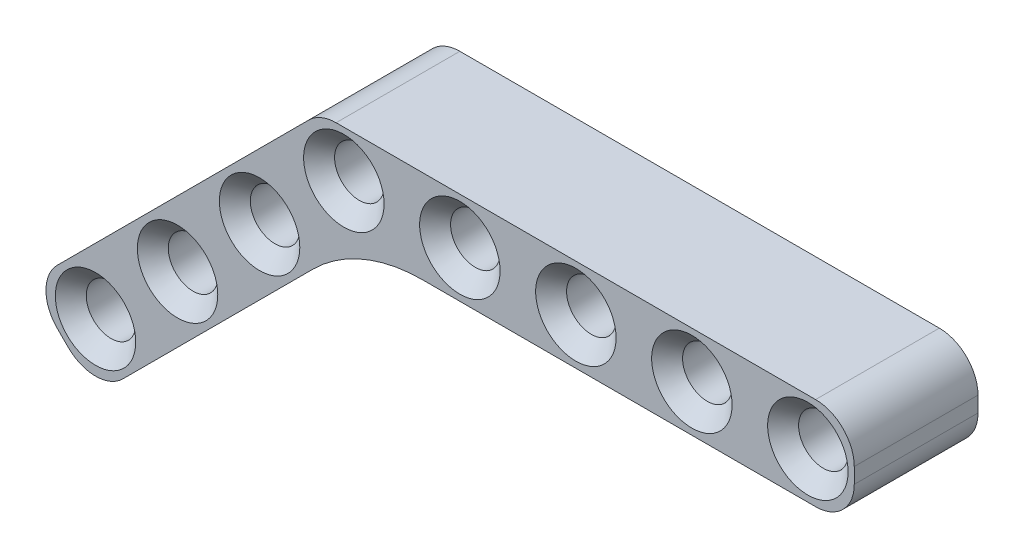
SolidWorks part; units mm, degrees
ref_plane "Front Plane" through (0, 0, 0) normal (0, 0, 1) x (1, 0, 0)
ref_plane "Top Plane" through (0, 0, 0) normal (0, 1, 0) x (1, 0, 0)
ref_plane "Right Plane" through (0, 0, 0) normal (1, 0, 0) x (0, 0, -1)
sketch "Sketch1" plane through (0, 0, 0) normal (0, 0, 1) x (1, 0, 0)
  line L1 (-0.5, 3) -> (30.5, 3)
  line L2 (-3, 0.5) -> (-3, -0.5)
  line L3 (-0.5, -3) -> (30.5, -3)
  line L4 (33, 0.5) -> (33, -0.5)
  circle A0 centre (0, 0) radius 1.6
  arc A1 (30.5, -3) -> (33, -0.5) centre (30.5, -0.5) ccw
  arc A2 (30.5, 3) -> (33, 0.5) centre (30.5, 0.5) cw
  arc A3 (-3, -0.5) -> (-0.5, -3) centre (-0.5, -0.5) ccw
  arc A4 (-0.5, 3) -> (-3, 0.5) centre (-0.5, 0.5) ccw
  circle A5 centre (7.5, 0) radius 1.6
  circle A6 centre (15, 0) radius 1.6
  circle A7 centre (22.5, 0) radius 1.6
  circle A8 centre (30, 0) radius 1.6
  point P8 (-3, 0)
  point P14 (-3, -3)
  point P17 (-3, 3)
  dimension "D1" = 3.2
  dimension "D4" = 2.5
  dimension "D2" = 6
  dimension "D3" = 3
  dimension "D6" = 7.5
  dimension "D5" = 5
extrude "Boss-Extrude1" add sketch "Sketch1" along normal blind 8
chamfer "Chamfer1" distance 1 angle 45 10 edges at (31.6, 0, 0) (31.6, 0, 8) (24.1, 0, 0) (24.1, 0, 8) (16.6, 0, 0) (16.6, 0, 8) (9.1, 0, 0) (9.1, 0, 8) (1.6, 0, 0) (1.6, 0, 8)
sketch "Sketch2" plane through (0, 0, 8) normal (0, 0, 1) x (1, 0, 0)
  line L0 (-2.2678, 2.2678) -> (-18.5292, -13.9937)
  line L1 (-18.5292, -17.5292) -> (-17.8221, -18.2363)
  line L2 (-14.2866, -18.2363) -> (0.9497, -3)
  line L4 (-0.5, -3) -> (30.5, -3) construction
  arc A0 (-0.5, 3) -> (-3, 0.5) centre (-0.5, 0.5) ccw construction
  circle A1 centre (-5.4477, -5.1548) radius 1.6
  circle A2 centre (-10.751, -10.4581) radius 1.6
  circle A3 centre (-16.0543, -15.7614) radius 1.6
  arc A4 (-18.5292, -13.9937) -> (-18.5292, -17.5292) centre (-16.7614, -15.7614) ccw
  arc A5 (-17.8221, -18.2363) -> (-14.2866, -18.2363) centre (-16.0543, -16.4685) ccw
  point P18 (-20.297, -15.7614)
  point P21 (-16.0543, -20.0041)
  arc M15 (-0.5, 3) -> (-3, 0.5) centre (-0.5, 0.5) ccw
  line M16 (-3, 0.5) -> (-3, -0.5)
  arc M17 (-3, -0.5) -> (-0.5, -3) centre (-0.5, -0.5) ccw
  line M18 (-0.5, -3) -> (30.5, -3)
  dimension "D3" = 3.2
  dimension "D8" = 2.5
  dimension "D1" = 6
  dimension "D2" = 45
  dimension "D4" = 3
  dimension "D5" = 7.5
  dimension "D7" = 3
  dimension "D6" = 3
extrude "Boss-Extrude3" add sketch "Sketch2" against normal blind 8 contours L1 A5 L2 L0 A4 A1 A2 A3 M18 M17 M16 M15
fillet "Fillet1" radius 10 1 edges at (0.9497, -3, 4)
chamfer "Chamfer2" distance 1 angle 45 6 edges at (-14.4543, -15.7614, 8) (-14.4543, -15.7614, 0) (-9.151, -10.4581, 8) (-9.151, -10.4581, 0) (-3.8477, -5.1548, 8) (-3.8477, -5.1548, 0)
